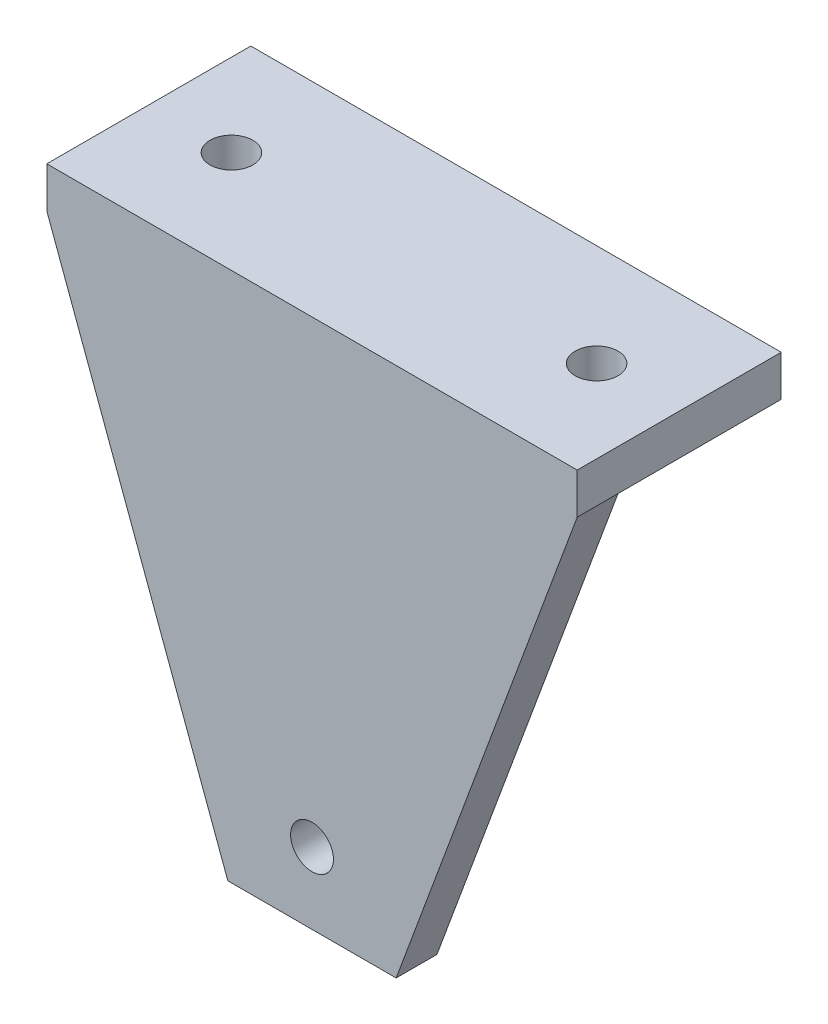
SolidWorks part; units mm, degrees
ref_plane "Front Plane" through (0, 0, 0) normal (0, 0, 1) x (1, 0, 0)
ref_plane "Top Plane" through (0, 0, 0) normal (0, 1, 0) x (1, 0, 0)
ref_plane "Right Plane" through (0, 0, 0) normal (1, 0, 0) x (0, 0, -1)
sketch "Sketch1" plane through (0, 0, 0) normal (0, 1, 0) x (1, 0, 0)
  line L0 (26, 20) -> (26, 0) construction
  line L1 (0, 0) -> (52, 0)
  line L2 (0, 0) -> (0, 20)
  line L3 (0, 20) -> (52, 20)
  line L4 (52, 0) -> (52, 20)
  line L5 (0, 10) -> (52, 10) construction
  circle A0 centre (43.9, 10) radius 2.1
  circle A1 centre (8.1, 10) radius 2.1
  dimension "D3" = 4.2
  dimension "D4" = 31.6
  dimension "D1" = 52
  dimension "D2" = 20
extrude "Boss-Extrude1" add sketch "Sketch1" along normal blind 4
sketch "Sketch2" plane through (0, 0, 0) normal (0, -1, 0) x (1, 0, 0)
  line L0 (0, -20) -> (0, 0) construction
  line L1 (52, 0) -> (0, 0)
  line L2 (52, 0) -> (52, -4)
  line L3 (52, -4) -> (0, -4)
  line L4 (0, 0) -> (0, -4)
  dimension "D1" = 4
extrude "Boss-Extrude2" add sketch "Sketch2" along normal blind 48
sketch "Sketch3" plane through (0, 0, 0) normal (0, 0, 1) x (1, 0, 0)
  line L0 (26, -48) -> (26, 4) construction
  line L1 (52, -48) -> (0, -48) construction
  line L2 (0, 4) -> (52, 4) construction
  line L3 (52, 0) -> (34.25, -48)
  line L4 (52, 4) -> (52, -48) construction
  line L5 (0, -48) -> (0, 0)
  line L7 (17.75, -48) -> (0, -48)
  line L8 (34.25, -48) -> (52, -48)
  line L9 (52, -48) -> (52, 0)
  line L10 (0, 0) -> (17.75, -48)
  circle A0 centre (26, -41) radius 2.1
  dimension "D2" = 4.2
  dimension "D3" = 7
  dimension "D1" = 4
  dimension "D4" = 16.5
extrude "Cut-Extrude1" cut sketch "Sketch3" against normal up to next
sketch "Sketch5" plane through (0, 0, -4) normal (0, 0, -1) x (-1, 0, 0)
  line L0 (-34.25, -48) -> (-38.0123, 0)
  line L1 (0, 0) -> (-52, 0) construction
  line L2 (-38.0123, 0) -> (-34, 0)
  line L3 (-34, 0) -> (-30.2377, -48)
  line L4 (-17.75, -48) -> (-34.25, -48) construction
  line L5 (-34.25, -48) -> (-30.2377, -48)
  line L6 (-26, -48) -> (-26, 0) construction
  line L7 (-13.9877, 0) -> (-18, 0)
  line L8 (-17.75, -48) -> (-13.9877, 0)
  line L9 (-18, 0) -> (-21.7623, -48)
  line L10 (-17.75, -48) -> (-21.7623, -48)
  dimension "D1" = 4
  dimension "D2" = 16
extrude "Boss-Extrude3" add sketch "Sketch5" along normal blind 16
sketch "Sketch6" plane through (0, 0, 0) normal (-1, 0, 0) x (0, 0, 1)
  line L0 (-20, 0) -> (-4, -48)
  line L4 (-20, -48) -> (-4, -48) construction
  line L5 (-20, 0) -> (-20, -48)
  line L6 (-20, -48) -> (-4, -48)
  line L7 (-4, -48) -> (-4, 0) construction
extrude "Cut-Extrude3" cut sketch "Sketch6" against normal through all
